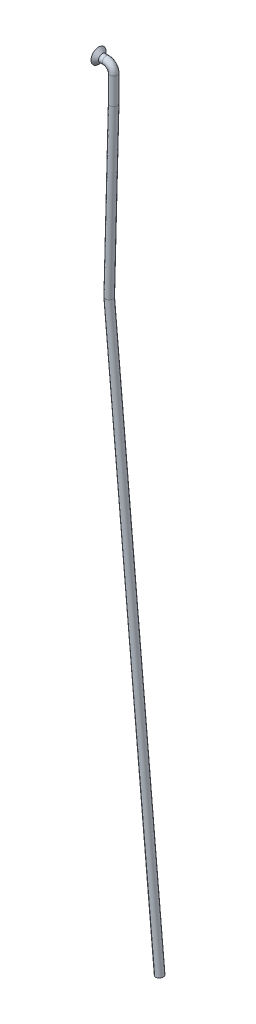
SolidWorks part; units mm, degrees
ref_plane "Plan de face" through (0, 0, 0) normal (0, 0, 1) x (1, 0, 0)
ref_plane "Plan de dessus" through (0, 0, 0) normal (0, 1, 0) x (1, 0, 0)
ref_plane "Plan de droite" through (0, 0, 0) normal (1, 0, 0) x (0, 0, -1)
sketch "Esquisse1" plane through (0, 0, 0) normal (0, 0, 1) x (1, 0, 0)
  line L0 (-1.178, -53.9846) -> (12.195, -203.0341)
  line L1 (-2, 0) -> (-4, 0)
  line L2 (0, -2) -> (0, -9)
  line L3 (0, -9) -> (-1.178, -53.9846)
  arc A0 (0, -2) -> (-2, 0) centre (-2, -2) ccw
  point P6 (0, 0)
  dimension "D3" = 2
  dimension "D1" = 4
  dimension "D2" = 88.5
  dimension "D4" = 203.4
  dimension "D5" = 7
  dimension "D6" = 45
  dimension "D7" = 17.27
ref_plane "Plan1" through (-4, 0, 0) normal (1, 0, 0) x (0, 0, -1)
sketch "Esquisse2" plane through (-4, 0, 0) normal (1, 0, 0) x (0, 0, -1)
  circle A0 centre (0, 0) radius 1
  dimension "D1" = 2
sweep "Balayage1" add profiles "Esquisse2" path "Esquisse1"
sketch "Esquisse3" plane through (0, 0, 0) normal (0, 0, 1) x (1, 0, 0)
  line L0 (-4, 1) -> (-4, 2)
  line L1 (-4, 2) -> (-3, 1)
  line L2 (-3, 1) -> (-4, 1)
  line L3 (-2, 1) -> (-4, 1) construction
  line L4 (-4, 1) -> (-4, -1) construction
  line L5 (0, 0) -> (-9.5023, 0) construction
  line L6 (-2, 0) -> (-4, 0) construction
  dimension "D1" = 4
  dimension "D2" = 1
revolve "Révolution1" add sketch "Esquisse3" angle 360 about L5
